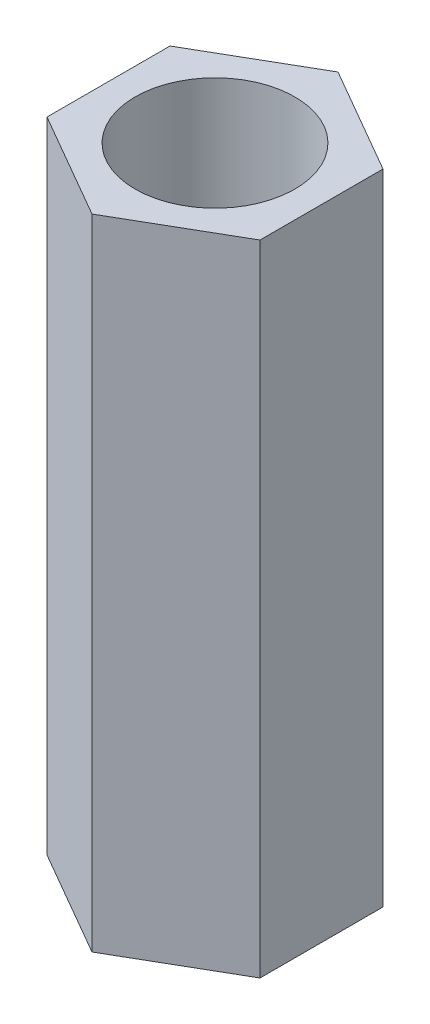
SolidWorks part; units mm, degrees
ref_plane "前视基准面" through (0, 0, 0) normal (0, 0, 1) x (1, 0, 0)
ref_plane "上视基准面" through (0, 0, 0) normal (0, 1, 0) x (1, 0, 0)
ref_plane "右视基准面" through (0, 0, 0) normal (1, 0, 0) x (0, 0, -1)
sketch "草图1" plane through (0, 0, 0) normal (0, 1, 0) x (1, 0, 0)
  line L1 (0, 2.3094) -> (-2, 1.1547)
  line L2 (-2, 1.1547) -> (-2, -1.1547)
  line L3 (-2, -1.1547) -> (0, -2.3094)
  line L4 (0, -2.3094) -> (2, -1.1547)
  line L5 (2, -1.1547) -> (2, 1.1547)
  line L6 (2, 1.1547) -> (0, 2.3094)
  circle A0 centre (0, 0) radius 2 construction
  circle A1 centre (0, 0) radius 1.5
  dimension "D1" = 3
  dimension "D2" = 4
extrude "凸台-拉伸1" add sketch "草图1" along normal blind 12
cosmetic thread "装饰螺纹线1" parameters "D2"=4
